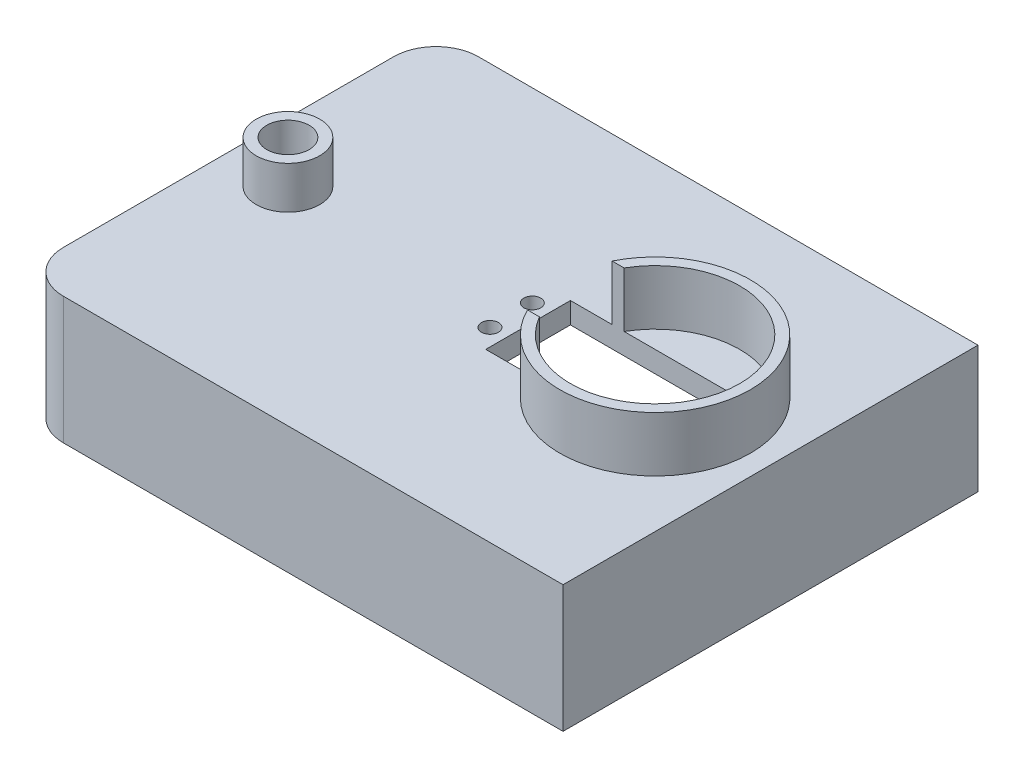
SolidWorks part; units mm, degrees
ref_plane "Alzado" through (0, 0, 0) normal (0, 0, 1) x (1, 0, 0)
ref_plane "Planta" through (0, 0, 0) normal (0, 1, 0) x (1, 0, 0)
ref_plane "Vista lateral" through (0, 0, 0) normal (1, 0, 0) x (0, 0, -1)
sketch "Croquis1" plane through (0, 0, 0) normal (0, 1, 0) x (1, 0, 0)
  line L1 (-64, 49) -> (64, 49)
  line L2 (-64, 49) -> (-64, -49)
  line L3 (-64, -49) -> (64, -49)
  line L4 (64, 49) -> (64, -49)
  line L5 (-64, 49) -> (64, -49) construction
  line L6 (-64, -49) -> (64, 49) construction
  line L7 (-59, 44) -> (59, 44)
  line L8 (-59, 44) -> (-59, -44)
  line L9 (-59, -44) -> (59, -44)
  line L10 (59, 44) -> (59, -44)
  line L11 (-59, 44) -> (59, -44) construction
  line L12 (-59, -44) -> (59, 44) construction
  point P0 (0, 0)
  point P6 (0, 0)
  dimension "D1" = 98
  dimension "D2" = 128
  dimension "D3" = 88
  dimension "D4" = 118
extrude "Saliente-Extruir5" add sketch "Croquis1" along normal blind 30
sketch "Croquis6" plane through (0, 30, 0) normal (0, 1, 0) x (1, 0, 0)
  line L1 (-64, 49) -> (64, 49)
  line L2 (-64, 49) -> (-64, -49)
  line L3 (-64, -49) -> (64, -49)
  line L4 (64, 49) -> (64, -49)
extrude "Saliente-Extruir6" add sketch "Croquis6" against normal blind 5
sketch "Croquis7" plane through (0, 30, 0) normal (0, 1, 0) x (1, 0, 0)
  line L5 (6.7401, 10) -> (46.7401, 10)
  line L6 (6.7401, 10) -> (6.7401, -10)
  line L7 (6.7401, -10) -> (46.7401, -10)
  line L8 (46.7401, 10) -> (46.7401, -10)
  line L11 (0, 0) -> (93.7234, 0) construction
  dimension "D1" = 40
  dimension "D2" = 20
  dimension "D3" = 10
extrude "Cortar-Extruir2" cut sketch "Croquis7" against normal blind 10
fillet "Redondeo1" radius 10 2 edges at (-64, 15, -49) (-64, 15, 49)
sketch "Croquis8" plane through (0, 30, 0) normal (0, 1, 0) x (1, 0, 0)
  circle A0 centre (50.7401, -5) radius 2
  circle A1 centre (50.7401, 5) radius 2
  circle A2 centre (2.7401, 5) radius 2
  circle A3 centre (2.7401, -5) radius 2
extrude "Cortar-Extruir3" cut sketch "Croquis8" against normal blind 10
sketch "Croquis9" plane through (0, 30, 0) normal (0, 1, 0) x (1, 0, 0)
  line L1 (16.5845, 10) -> (19.4196, 10)
  line L3 (16.5845, -10) -> (19.4196, -10)
  arc A0 (16.5845, -10) -> (16.5845, 10) centre (36.7401, 0) ccw
  arc A1 (19.4196, -10) -> (19.4196, 10) centre (36.7401, 0) ccw
  dimension "D1" = 45
  dimension "D2" = 40
extrude "Saliente-Extruir7" add sketch "Croquis9" along normal blind 13
sketch "Croquis11" plane through (0, 30, 0) normal (0, 1, 0) x (1, 0, 0)
  circle A0 centre (-49.9722, 0) radius 5
  dimension "D1" = 10
extrude "Cortar-Extruir4" cut sketch "Croquis11" against normal blind 60
sketch "Croquis12" plane through (0, 30, 0) normal (0, 1, 0) x (1, 0, 0)
  circle A0 centre (-49.9722, 0) radius 5
  circle A1 centre (-49.9722, 0) radius 7.5
  dimension "D1" = 15
extrude "Saliente-Extruir9" add sketch "Croquis12" along normal blind 10
